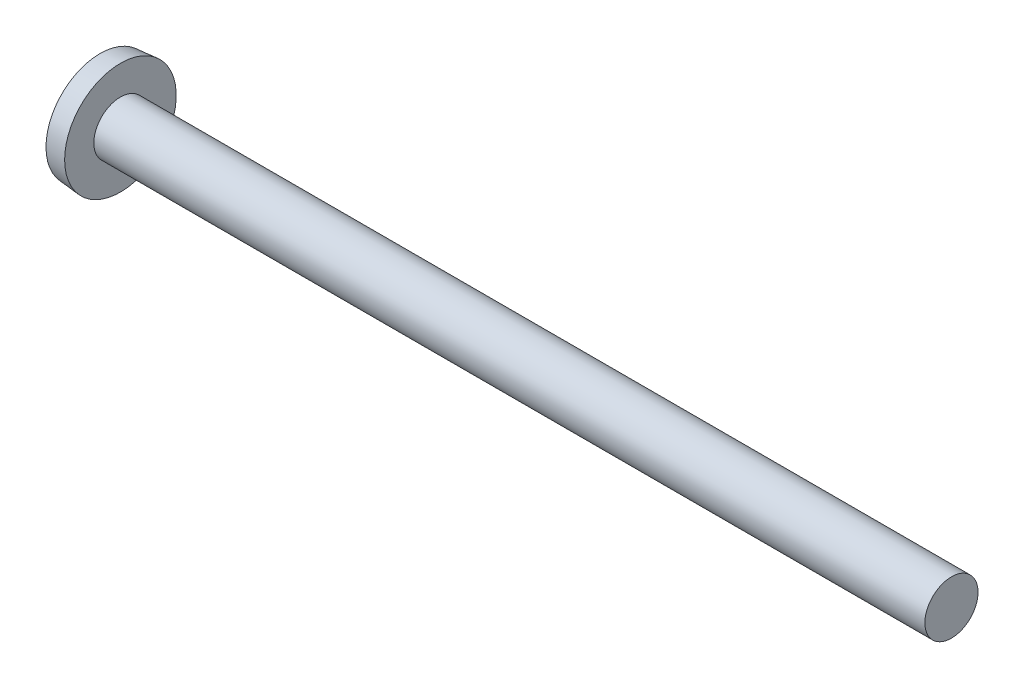
SolidWorks part; units mm, degrees
ref_plane "Plane1" through (0, 0, 0) normal (0, 0, 1) x (1, 0, 0)
ref_plane "Plane2" through (0, 0, 0) normal (0, 1, 0) x (1, 0, 0)
ref_plane "Plane3" through (0, 0, 0) normal (1, 0, 0) x (0, 0, -1)
sketch "BodySke" plane through (0, 0, 0) normal (0, 0, 1) x (1, 0, 0)
  line L0 (1.7272, 1.4224) -> (1.7272, 2.9845)
  line L1 (1.7272, 2.9845) -> (0.635, 2.8889)
  line L2 (-25.4, 0) -> (127, 0) construction
  line L3 (1.7272, -2.9845) -> (0.635, -2.8889) construction
  line L4 (1.7272, 1.4224) -> (46.1772, 1.4224)
  line L5 (46.1772, 1.4224) -> (46.1772, 0)
  line L6 (46.1772, 0) -> (0, 0)
  line L7 (1.7272, -1.4224) -> (46.1772, -1.4224) construction
  line L8 (2.2555, 6.35) -> (2.2555, -3.175) construction
  line L9 (1.7272, 6.35) -> (1.7272, -3.175) construction
  arc A0 (0, 0) -> (0.635, 2.8889) centre (6.8892, 0) cw
  dimension "Head_ang" = 85
  dimension "Oval_ht" = 0.635
  dimension "Head_ht" = 1.7272
  dimension "Diameter" = 2.8448
  dimension "Length" = 44.45
  dimension "Head_dia" = 5.969
  dimension "Advance" = 0.5283
  dimension "Thread_nom" = 44.45
revolve "Base-Revolve" add sketch "BodySke" angle 360 about L2
cosmetic thread "ThreadCosmetic" [suppressed] parameters "Thread_length"=43.9217, "Thread_minor"=2.2123
sketch "Sketch2" plane through (0, 0, 0) normal (1, 0, 0) x (0, 0, -1)
  line L0 (2.9845, -0.4953) -> (2.9845, 0.4953)
  line L1 (2.9845, 0.4953) -> (-2.9845, 0.4953)
  line L2 (-2.9845, 0.4953) -> (-2.9845, -0.4953)
  line L3 (-2.9845, -0.4953) -> (2.9845, -0.4953)
  dimension "D1" = 5.969
  dimension "D2" = 2.9845
  dimension "D3" = 0.4953
  dimension "Slot_width" = 0.9906
extrude "Slot" [suppressed] cut sketch "Sketch2" along normal blind 1.0668
sketch "Sketch3" plane through (0, 0, 0) normal (1, 0, 0) x (0, 0, -1)
  line L0 (-0.4318, 1.9558) -> (0.4318, 1.9558)
  line L1 (0.4318, 1.9558) -> (0.4318, -1.9558)
  line L2 (0.4318, -1.9558) -> (-0.4318, -1.9558)
  line L3 (-0.4318, -1.9558) -> (-0.4318, 1.9558)
  dimension "Cross_width" = 0.8636
  dimension "D1" = 0.4318
  dimension "Cross_dia" = 3.9116
  dimension "D2" = 1.9558
ref_plane "Plane4" through (2.1844, 0, 0) normal (1, 0, 0) x (0, 0, -1)
sketch "Sketch4" plane through (2.1844, 0, 0) normal (1, 0, 0) x (0, 0, -1)
  line L0 (-0.2159, 0.2159) -> (0.2159, 0.2159)
  line L1 (0.2159, 0.2159) -> (0.2159, -0.2159)
  line L2 (0.2159, -0.2159) -> (-0.2159, -0.2159)
  line L3 (-0.2159, -0.2159) -> (-0.2159, 0.2159)
  dimension "D1" = 0.4318
  dimension "D2" = 0.2159
  dimension "D3" = 0.4318
  dimension "D4" = 0.2159
loft "Cross" cut profiles "Sketch3", "Sketch4"
pattern_circular "CirPattern1" count 2 every 90 about axis through (0, 0, 0) along (1, 0, 0) of "Cross"
sketch "ThdSchSke" plane through (0, 0, 0) normal (0, 0, 1) x (1, 0, 0)
  line L0 (2.2555, -1.1062) -> (2.0341, -1.4224)
  line L1 (2.2555, -1.1062) -> (2.4769, -1.4224)
  line L2 (2.4769, -1.4224) -> (2.4769, -1.778)
  line L3 (-3.175, 0) -> (5.1513, 0) construction
  line L5 (2.4769, -1.778) -> (2.0341, -1.778)
  line L6 (2.0341, -1.778) -> (2.0341, -1.4224)
  dimension "Diameter" = 2.8448
  dimension "SideAngle" = 55
  dimension "VeeAngle" = 70
  dimension "Thread_minor" = 2.2123
  dimension "Overcut" = 3.556
  dimension "Start" = 2.2555
revolve "ThreadSchematic" [suppressed] cut sketch "ThdSchSke" angle 360 about L3
pattern_linear "ThdSchPat" [suppressed]
equation "\"D1@Sketch3\" = \"Cross_width@Sketch3\" / 2"
equation "\"D2@Sketch3\" = \"Cross_dia@Sketch3\" / 2"
equation "\"D1@Sketch4\" = \"Cross_width@Sketch3\"*.5"
equation "\"D2@Sketch4\" = \"D1@Sketch4\" / 2"
equation "\"D3@Sketch4\" = \"D1@Sketch4\""
equation "\"D4@Sketch4\" = \"D2@Sketch4\""
equation "\"D1@Sketch2\" = \"Head_dia@BodySke\""
equation "\"D2@Sketch2\" = \"D1@Sketch2\" / 2"
equation "\"D3@Sketch2\" = \"Slot_width@Sketch2\" / 2"
equation "\"Thread_length@ThreadCosmetic\" = ((sgn( (\"Length@BodySke\" - \"Advance@BodySke\" ) - \"Thread_nom@BodySke\" )-1)*( (\"Length@BodySke\" - \"Advance@BodySke\" ) - \"Thread_nom@BodySke\" ))/-2+ \"Thread_nom@BodySke\""
equation "\"Thread_minor@ThdSchSke\" = \"Thread_minor@ThreadCosmetic\""
equation "\"Diameter@ThdSchSke\" = \"Diameter@BodySke\""
equation "\"Overcut@ThdSchSke\" = \"Diameter@BodySke\" * 1.25"
equation "\"Start@ThdSchSke\" = \"Head_ht@BodySke\" + \"Length@BodySke\" - \"Thread_length@ThreadCosmetic\"  '---Non-countersunk---"
equation "\"Num_threads@ThdSchPat\" = int( \"Thread_length@ThreadCosmetic\" / \"Advance@BodySke\" + 0.999 )  + 1"
equation "\"Advance@ThdSchPat\" = \"Thread_length@ThreadCosmetic\" /  (\"Num_threads@ThdSchPat\" - 1) 'relax it"
